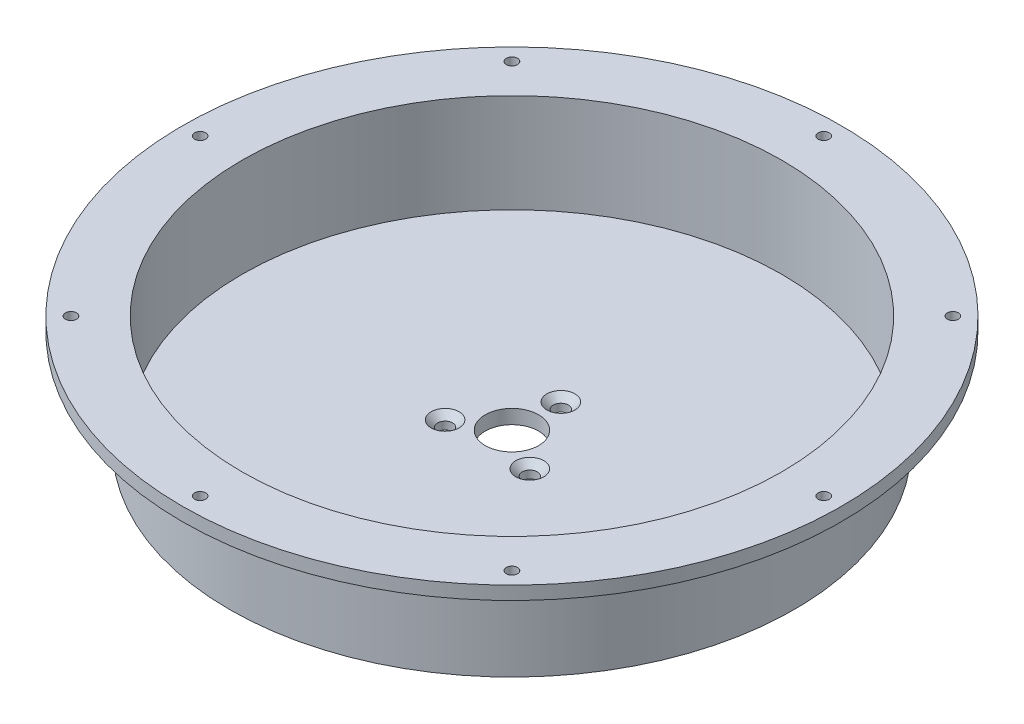
SolidWorks part; units mm, degrees
material "6061 Alloy"
ref_plane "Front Plane" through (0, 0, 0) normal (0, 0, 1) x (1, 0, 0)
ref_plane "Top Plane" through (0, 0, 0) normal (0, 1, 0) x (1, 0, 0)
ref_plane "Right Plane" through (0, 0, 0) normal (1, 0, 0) x (0, 0, -1)
sketch "Sketch1" plane through (0, 0, 0) normal (0, 1, 0) x (1, 0, 0)
  circle A0 centre (0, 0) radius 59.69 construction
  circle A1 centre (0, 0) radius 60.69
  circle A2 centre (0, 0) radius 63.5
  dimension "D1" = 127
  dimension "D2" = 121.38
  dimension "D3" = 119.38
  dimension "D4" = 0
extrude "Boss-Extrude1" add sketch "Sketch1" along normal blind 25.4 contours A2 | A1
sketch "Sketch3" plane through (0, 0, 0) normal (0, 1, 0) x (1, 0, 0)
  circle A0 centre (0, 0) radius 63.5
extrude "Boss-Extrude2" add sketch "Sketch3" along normal blind 3.175
sketch "Sketch8" plane through (0, 0, 0) normal (0, -1, 0) x (1, 0, 0)
  circle A0 centre (0, 0) radius 6
  dimension "D1" = 12
extrude "Cut-Extrude1" cut sketch "Sketch8" against normal up to next
sketch "Sketch9" plane through (0, 25.4, 0) normal (0, 1, 0) x (1, 0, 0)
  circle A0 centre (0, 0) radius 63.5
  circle A1 centre (0, 0) radius 74.095
  dimension "D1" = 127
  dimension "D2" = 148.19
extrude "Boss-Extrude4" add sketch "Sketch9" against normal blind 3
sketch "Sketch12" plane through (0, 25.4, 0) normal (0, 1, 0) x (1, 0, 0)
  point P0 (0, 70.1)
  dimension "D1" = 70.1
hole_wizard "M3x0.5 Tapped Hole1" positions "Sketch12" profile "Sketch11" tap size "M3x0.5" standard "ANSI Metric" end condition through all
sketch "Sketch11" plane through (0, 25.4, -70.1) normal (1, 0, 0) x (0, 0, 1)
  line L0 (0, 0) -> (0, 25.4)
  line L1 (0, 25.4) -> (1.25, 25.4)
  line L2 (1.25, 25.4) -> (1.25, 0)
  line L5 (1.25, 0) -> (0, 0)
  line L11 (0, -6.35) -> (0, 107.95) construction
  dimension "Thru Tap Drill Dia." = 2.5
  dimension "Thru Tap Drill Depth" = 25.4
cosmetic thread "Hole Thread1" parameters "D2"=3
pattern_circular "CirPattern2" count 8 over 360 about axis through (0, 0, 0) along (0, 1, 0) of "M3x0.5 Tapped Hole1"
cosmetic thread "Hole Thread2" parameters "D2"=3
cosmetic thread "Hole Thread3" parameters "D2"=3
cosmetic thread "Hole Thread4" parameters "D2"=3
cosmetic thread "Hole Thread5" parameters "D2"=3
cosmetic thread "Hole Thread6" parameters "D2"=3
cosmetic thread "Hole Thread7" parameters "D2"=3
cosmetic thread "Hole Thread8" parameters "D2"=3
fillet "Fillet1" radius 3 1 edges at (0, 22.4, 63.5)
sketch "Sketch16" plane through (0, 3.175, 0) normal (0, 1, 0) x (1, 0, 0)
  point P0 (0, 11)
  dimension "D1" = 11
hole_wizard "CSK for M3 Flat Head Machine Screw1" positions "Sketch16" profile "Sketch15" countersink size "M3" standard "ANSI Metric" end condition through all
sketch "Sketch15" plane through (0, 3.175, -11) normal (1, 0, 0) x (0, 0, 1)
  line L0 (0, 0) -> (0, 3.175)
  line L1 (0, 3.175) -> (1.7, 3.175)
  line L2 (1.7, 3.175) -> (1.7, 1.45)
  line L3 (1.7, 1.45) -> (3.15, 0)
  line L5 (3.15, 0) -> (0, 0)
  line L6 (-1.7, 1.45) -> (-3.15, 0) construction
  line L11 (0, -6.35) -> (0, 107.95) construction
  dimension "Thru Hole Dia." = 3.4
  dimension "Thru Hole Depth" = 3.175
  dimension "Near C'Sink Dia." = 6.3
  dimension "Near C'Sink Angle" = 90
pattern_circular "CirPattern3" count 3 over 360 about axis through (0, 0, 0) along (0, 1, 0) of "CSK for M3 Flat Head Machine Screw1"
